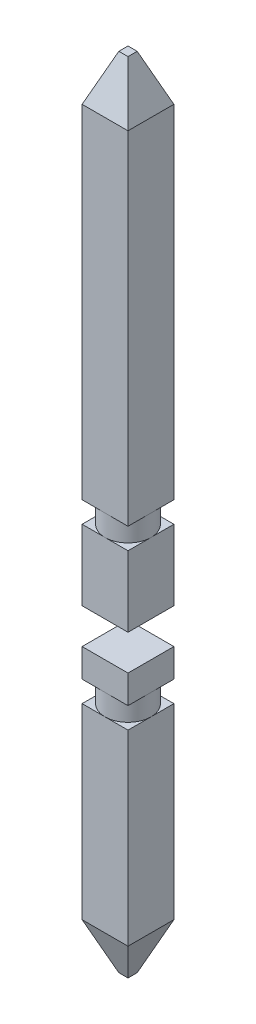
SolidWorks part; units mm, degrees
ref_plane "Front Plane" through (0, 0, 0) normal (0, 0, 1) x (1, 0, 0)
ref_plane "Top Plane" through (0, 0, 0) normal (0, 1, 0) x (1, 0, 0)
ref_plane "Right Plane" through (0, 0, 0) normal (1, 0, 0) x (0, 0, -1)
sketch "Sketch2" plane through (0, 0, 0) normal (0, 1, 0) x (1, 0, 0)
  line L1 (-0.325, -0.325) -> (0.325, -0.325)
  line L2 (-0.325, -0.325) -> (-0.325, 0.325)
  line L3 (-0.325, 0.325) -> (0.325, 0.325)
  line L4 (0.325, -0.325) -> (0.325, 0.325)
  line L5 (-0.325, -0.325) -> (0.325, 0.325) construction
  line L6 (-0.325, 0.325) -> (0.325, -0.325) construction
  point P0 (0, 0)
  dimension "D1" = 0.65
  dimension "D2" = 0.65
extrude "Boss-Extrude1" add sketch "Sketch2" along normal blind 11.3
sketch "Sketch6" plane through (0, 0, 0.325) normal (0, 0, 1) x (1, 0, 0)
  line L0 (-0.325, 11.3) -> (-0.325, 0) construction
  line L1 (-0.325, 4.5) -> (0.325, 4.5)
  line L2 (-0.325, 4.5) -> (-0.325, 4)
  line L3 (-0.325, 4) -> (0.325, 4)
  line L4 (0.325, 4.5) -> (0.325, 4)
  line L5 (0.325, 11.3) -> (0.325, 0) construction
  line L6 (-0.325, 0) -> (0.325, 0) construction
  dimension "D1" = 4
  dimension "D2" = 0.5
extrude "Cut-Extrude1" cut sketch "Sketch6" against normal through all
sketch "Sketch7" plane through (0, 0, 0.325) normal (0, 0, 1) x (1, 0, 0)
  line L0 (-0.325, 4) -> (-0.325, 0) construction
  line L1 (-0.325, 3.3) -> (0.325, 3.3)
  line L2 (-0.325, 3.3) -> (-0.325, 3.6)
  line L3 (-0.325, 3.6) -> (0.325, 3.6)
  line L4 (0.325, 3.3) -> (0.325, 3.6)
  line L5 (0.325, 4) -> (0.325, 0) construction
  line L7 (-0.325, 4) -> (0.325, 4) construction
  dimension "D1" = 0.3
  dimension "D2" = 0.4
extrude "Cut-Extrude2" cut sketch "Sketch7" against normal through all
sketch "Sketch8" plane through (0, 3.3, 0) normal (0, 1, 0) x (1, 0, 0)
  circle A0 centre (0, 0) radius 0.325
extrude "Boss-Extrude2" add sketch "Sketch8" along normal up to surface (0.3 mm away) up to face at (0, 3.6, 0)
sketch "Sketch9" plane through (0, 0, 0.325) normal (0, 0, 1) x (1, 0, 0)
  line L0 (-0.325, 11.3) -> (-0.325, 4.5) construction
  line L1 (-0.325, 5.5) -> (0.325, 5.5)
  line L2 (-0.325, 5.5) -> (-0.325, 5.8)
  line L3 (-0.325, 5.8) -> (0.325, 5.8)
  line L4 (0.325, 5.5) -> (0.325, 5.8)
  line L5 (0.325, 11.3) -> (0.325, 4.5) construction
  line L6 (0.325, 4.5) -> (-0.325, 4.5) construction
  dimension "D1" = 1
  dimension "D2" = 0.3
extrude "Cut-Extrude3" cut sketch "Sketch9" against normal through all
sketch "Sketch10" plane through (0, 5.5, 0) normal (0, 1, 0) x (1, 0, 0)
  circle A0 centre (0, 0) radius 0.325
extrude "Boss-Extrude3" add sketch "Sketch10" along normal up to surface (0.3 mm away) up to face at (0, 5.8, 0)
chamfer "Chamfer1" distance 0.65 distance2 0.26 4 edges at (0, 11.3, -0.325) (-0.325, 11.3, 0) (0, 11.3, 0.325) (0.325, 11.3, 0)
chamfer "Chamfer2" distance 0.26 distance2 0.65 4 edges at (0, 0, -0.325) (-0.325, 0, 0) (0, 0, 0.325) (0.325, 0, 0)
fillet "Fillet1" [suppressed] radius 0.01
fillet "Fillet2" [suppressed] radius 0.01
